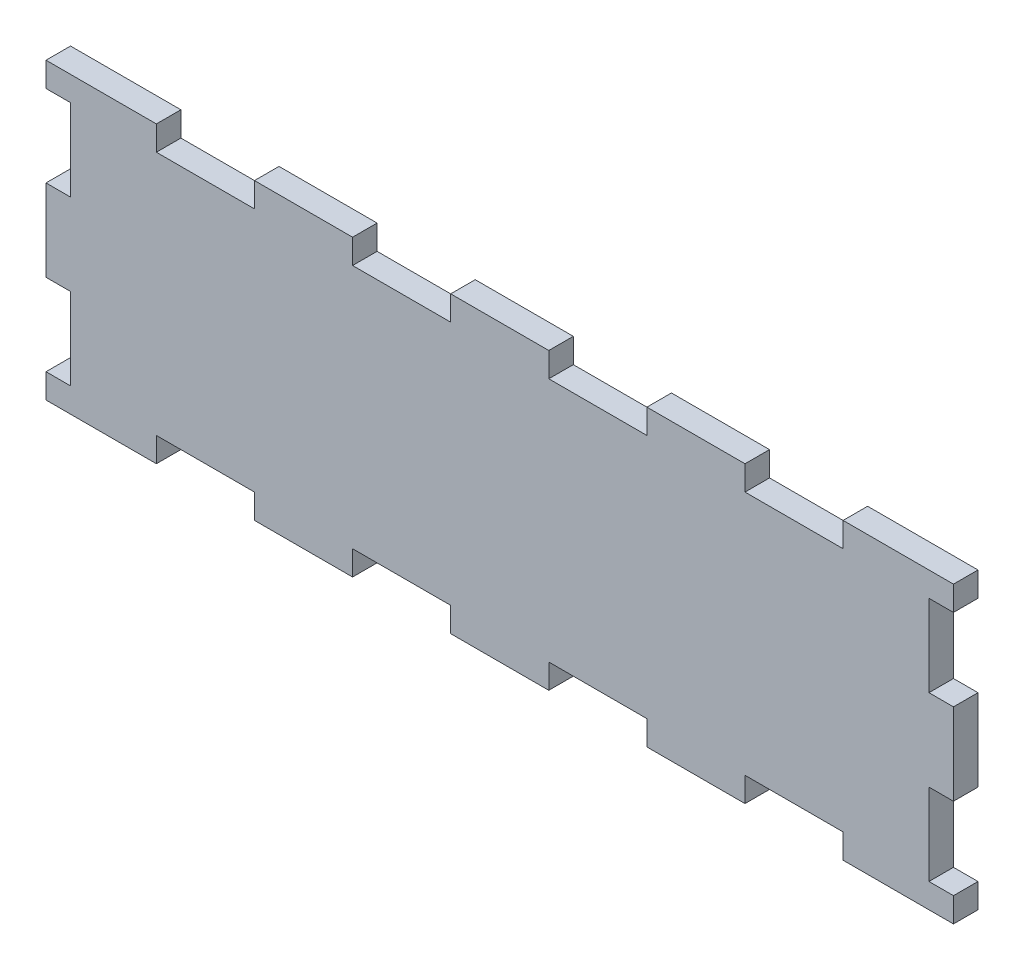
SolidWorks part; units mm, degrees
ref_plane "Front Plane" through (0, 0, 0) normal (0, 0, 1) x (1, 0, 0)
ref_plane "Top Plane" through (0, 0, 0) normal (0, 1, 0) x (1, 0, 0)
ref_plane "Right Plane" through (0, 0, 0) normal (1, 0, 0) x (0, 0, -1)
sketch "Sketch1" plane through (0, 0, 0) normal (0, 0, 1) x (1, 0, 0)
  line L0 (-84, 0) -> (-111, 0)
  line L1 (-111, 0) -> (-111, 6)
  line L2 (-111, 6) -> (-105, 6)
  line L3 (-105, 6) -> (-105, 26)
  line L4 (-105, 26) -> (-111, 26)
  line L5 (-111, 26) -> (-111, 46)
  line L6 (-111, 46) -> (-105, 46)
  line L7 (-105, 46) -> (-105, 66)
  line L8 (-105, 66) -> (-111, 66)
  line L9 (-111, 66) -> (-111, 72)
  line L10 (-111, 72) -> (-84, 72)
  line L11 (-84, 72) -> (-84, 66)
  line L12 (-84, 66) -> (-60, 66)
  line L13 (-60, 66) -> (-60, 72)
  line L14 (-60, 72) -> (-36, 72)
  line L15 (-36, 72) -> (-36, 66)
  line L16 (-36, 66) -> (-12, 66)
  line L17 (-12, 66) -> (-12, 72)
  line L18 (-12, 72) -> (12, 72)
  line L19 (12, 72) -> (12, 66)
  line L20 (12, 66) -> (36, 66)
  line L21 (36, 66) -> (36, 72)
  line L22 (36, 72) -> (60, 72)
  line L23 (60, 72) -> (60, 66)
  line L24 (60, 66) -> (84, 66)
  line L25 (84, 66) -> (84, 72)
  line L26 (84, 72) -> (111, 72)
  line L27 (111, 72) -> (111, 66)
  line L28 (111, 66) -> (105, 66)
  line L29 (105, 66) -> (105, 46)
  line L30 (105, 46) -> (111, 46)
  line L31 (111, 46) -> (111, 26)
  line L32 (111, 26) -> (105, 26)
  line L33 (105, 26) -> (105, 6)
  line L34 (105, 6) -> (111, 6)
  line L35 (111, 6) -> (111, 0)
  line L36 (111, 0) -> (84, 0)
  line L37 (84, 0) -> (84, 6)
  line L38 (60, 6) -> (60, 0)
  line L39 (60, 0) -> (36, 0)
  line L40 (36, 0) -> (36, 6)
  line L41 (36, 6) -> (12, 6)
  line L42 (12, 6) -> (12, 0)
  line L43 (12, 0) -> (-12, 0)
  line L44 (-12, 0) -> (-12, 6)
  line L45 (-36, 6) -> (-36, 0)
  line L46 (-36, 0) -> (-60, 0)
  line L47 (-60, 0) -> (-60, 6)
  line L48 (-60, 6) -> (-84, 6)
  line L49 (-84, 6) -> (-84, 0)
  line L50 (-36, 6) -> (-12, 6)
  line L51 (84, 6) -> (60, 6)
extrude "Boss-Extrude1" add sketch "Sketch1" along normal blind 6
